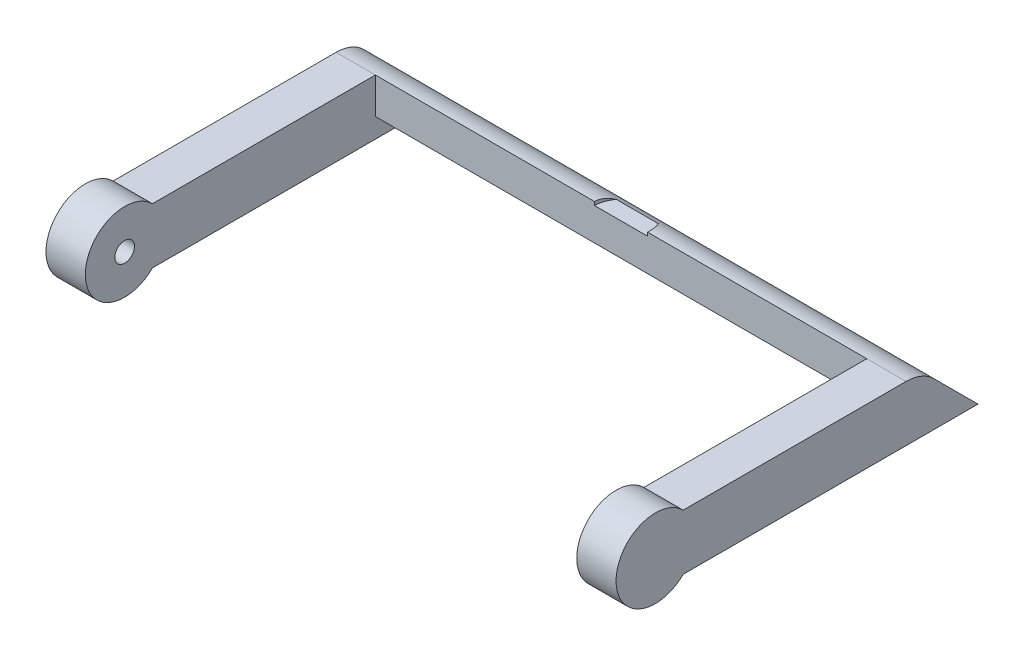
SolidWorks part; units mm, degrees
ref_plane "Alzado" through (0, 0, 0) normal (0, 0, 1) x (1, 0, 0)
ref_plane "Planta" through (0, 0, 0) normal (0, 1, 0) x (1, 0, 0)
ref_plane "Vista lateral" through (0, 0, 0) normal (1, 0, 0) x (0, 0, -1)
sketch "Croquis1" plane through (0, 0, 0) normal (1, 0, 0) x (0, 0, -1)
  line L0 (0, 0) -> (15, 0)
  line L1 (15, 0) -> (12.7574, 2.2426)
  line L2 (11.3431, 2.8284) -> (0, 2.8284)
  arc A0 (0, 2.8284) -> (0, 0) centre (-1.4142, 1.4142) ccw
  arc A1 (12.7574, 2.2426) -> (11.3431, 2.8284) centre (11.3431, 0.8284) ccw
  dimension "D4" = 2
  dimension "D2" = 2
  dimension "D1" = 15
  dimension "D3" = 45
extrude "Saliente-Extruir1" add sketch "Croquis1" along normal blind 29
ref_plane "Plano1" through (0, 2.8284, 0) normal (0, 1, 0) x (1, 0, 0)
sketch "Croquis2" plane through (0, 2.8284, 0) normal (0, 1, 0) x (1, 0, 0)
  line L0 (0, 0) -> (2, 0) construction
  line L1 (29, 0) -> (0, 0) construction
  line L2 (29, 0) -> (27, 0) construction
  line L3 (2, 0) -> (2, 11.3431)
  line L4 (29, 11.3431) -> (0, 11.3431) construction
  line L5 (2, 11.3431) -> (27, 11.3431)
  line L6 (27, 11.3431) -> (27, 0)
  line L7 (27, 0) -> (27, -11.3466)
  line L8 (2, 0) -> (2, -9.4581)
  line L9 (2, -9.4581) -> (27, -11.3466)
  dimension "D1" = 2
  dimension "D2" = 2
extrude "Cortar-Extruir1" cut sketch "Croquis2" against normal mid plane 29
chamfer "Chaflán1" distance 1 angle 45 1 edges at (14.5, 0, -11.3431)
sketch "Croquis3" plane through (27, 0, 0) normal (-1, 0, 0) x (0, 0, 1)
  line L0 (1.4142, 1.4142) -> (1.4142, 3.4142) construction
  arc A0 (0, 0) -> (0, 2.8284) centre (1.4142, 1.4142) ccw construction
  circle A1 centre (1.4142, 1.4142) radius 0.5
  dimension "D1" = 1
extrude "Cortar-Extruir2" cut sketch "Croquis3" against normal blind 1
sketch "Croquis4" plane through (2, 0, 0) normal (1, 0, 0) x (0, 0, -1)
  circle A0 centre (-1.4142, 1.4142) radius 0.5
  point P0 (-1.4142, 1.4142)
  dimension "D1" = 1
extrude "Cortar-Extruir3" cut sketch "Croquis4" against normal blind 1
ref_plane "Plano2" through (0, 2.85, 0) normal (0, 1, 0) x (1, 0, 0)
sketch "Croquis5" plane through (0, 2.85, 0) normal (0, 1, 0) x (1, 0, 0)
  line L0 (13.15, 11.3431) -> (15.85, 11.3431)
  arc A0 (15.85, 11.3431) -> (13.15, 11.3431) centre (14.5, 11.3431) ccw
extrude "Cortar-Extruir5" cut sketch "Croquis5" against normal blind 0.2
